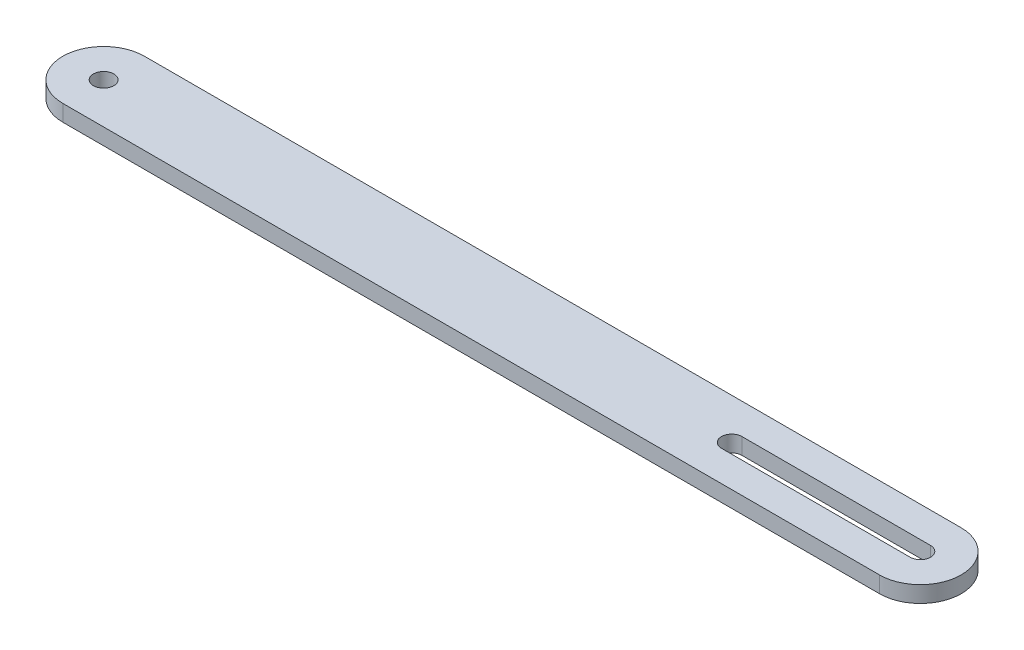
SolidWorks part; units mm, degrees
ref_plane "Front Plane" through (0, 0, 0) normal (0, 0, 1) x (1, 0, 0)
ref_plane "Top Plane" through (0, 0, 0) normal (0, 1, 0) x (1, 0, 0)
ref_plane "Right Plane" through (0, 0, 0) normal (1, 0, 0) x (0, 0, -1)
sketch "Sketch1" plane through (0, 0, 0) normal (0, 1, 0) x (1, 0, 0)
  line L0 (269, 12.5) -> (500, 12.5)
  line L1 (-500, 50) -> (500, 50)
  line L3 (-500, -50) -> (500, -50)
  line L5 (0, 0) -> (275, -12.5) construction
  line L7 (269, -12.5) -> (500, -12.5)
  line L8 (0, 0) -> (275, 12.5) construction
  arc A1 (500, -12.5) -> (500, 12.5) centre (500, 0) ccw
  arc A3 (-500, 50) -> (-500, -50) centre (-500, 0) ccw
  arc A4 (271.0982, 12.3226) -> (271.0982, -12.3226) centre (269, 0) ccw
  arc A5 (500, -50) -> (500, 50) centre (500, 0) ccw
  circle A6 centre (-500, 0) radius 12.5
  point P0 (0, 0)
  dimension "D2" = 50
  dimension "D5" = 25
  dimension "D1" = 231
  dimension "D3" = 1000
  dimension "D4" = 500
extrude "Boss-Extrude2" add sketch "Sketch1" along normal blind 20 contours L3 A5 L1 A3 A4 L0 A1 L7
